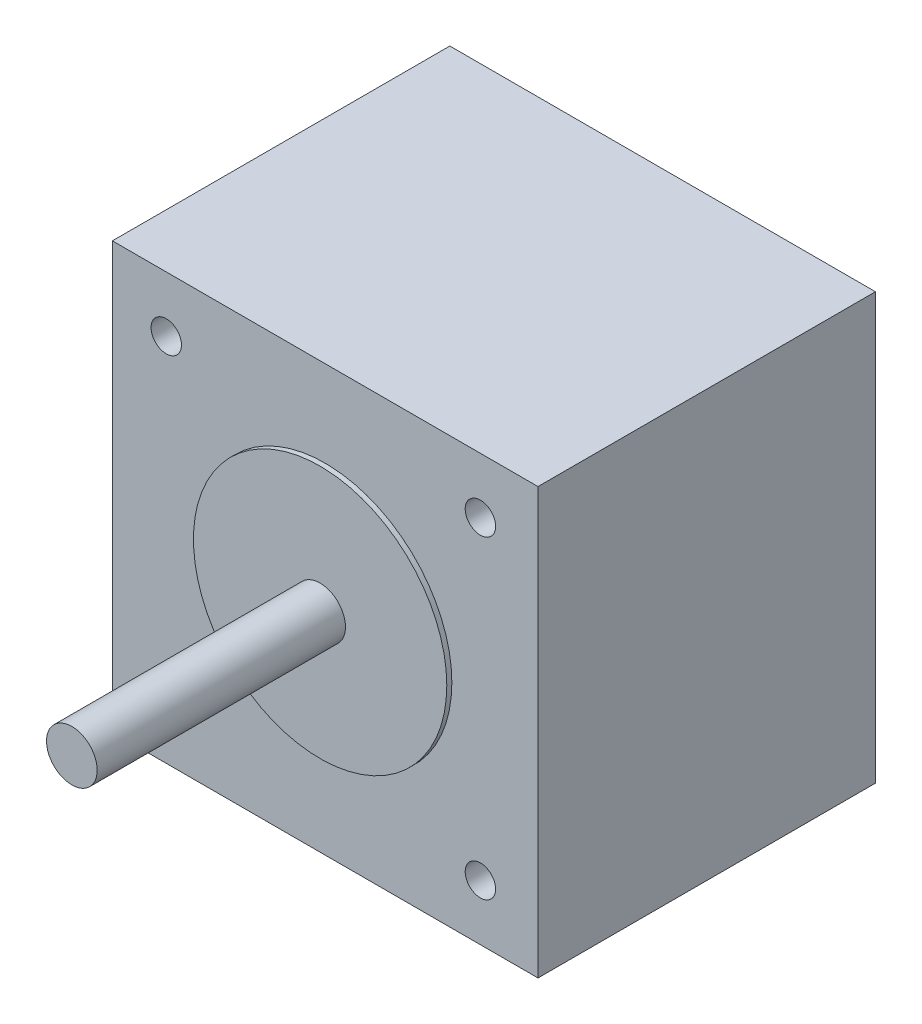
SolidWorks part; units mm, degrees
ref_plane "正面" through (0, 0, 0) normal (0, 0, 1) x (1, 0, 0)
ref_plane "平面" through (0, 0, 0) normal (0, 1, 0) x (1, 0, 0)
ref_plane "右側面" through (0, 0, 0) normal (1, 0, 0) x (0, 0, -1)
sketch "ｽｹｯﾁ1" plane through (0, 0, 0) normal (0, 0, 1) x (1, 0, 0)
  line L1 (21, -21) -> (-21, -21)
  line L2 (21, -21) -> (21, 21)
  line L3 (21, 21) -> (-21, 21)
  line L4 (-21, -21) -> (-21, 21)
  line L5 (21, -21) -> (-21, 21) construction
  line L6 (21, 21) -> (-21, -21) construction
  point P0 (0, 0)
  dimension "D1" = 42
  dimension "D2" = 42
extrude "ﾎﾞｽ - 押し出し1" add sketch "ｽｹｯﾁ1" along normal blind 33.3
sketch "ｽｹｯﾁ2" plane through (0, 0, 33.3) normal (0, 0, 1) x (1, 0, 0)
  circle A0 centre (0, 0) radius 12.5
  dimension "D1" = 25
extrude "ﾎﾞｽ - 押し出し2" add sketch "ｽｹｯﾁ2" along normal blind 0.5
sketch "ｽｹｯﾁ3" plane through (0, 0, 33.3) normal (0, 0, 1) x (1, 0, 0)
  circle A0 centre (-15.6825, 15.5) radius 1.5
  circle A1 centre (-15.6825, -15.5) radius 1.5
  circle A2 centre (15.3175, -15.5) radius 1.5
  circle A3 centre (15.3175, 15.5) radius 1.5
  dimension "D1" = 3
  dimension "D2" = 3
  dimension "D5" = 3
  dimension "D7" = 3
  dimension "D3" = 31
  dimension "D4" = 15.5
  dimension "D6" = 31
extrude "ｶｯﾄ - 押し出し1" cut sketch "ｽｹｯﾁ3" against normal blind 10
sketch "ｽｹｯﾁ5" plane through (0, 0, 33.3) normal (0, 0, 1) x (1, 0, 0)
  circle A0 centre (0, 0) radius 2.5
  dimension "D1" = 5
extrude "ﾎﾞｽ - 押し出し3" add sketch "ｽｹｯﾁ5" along normal blind 25
